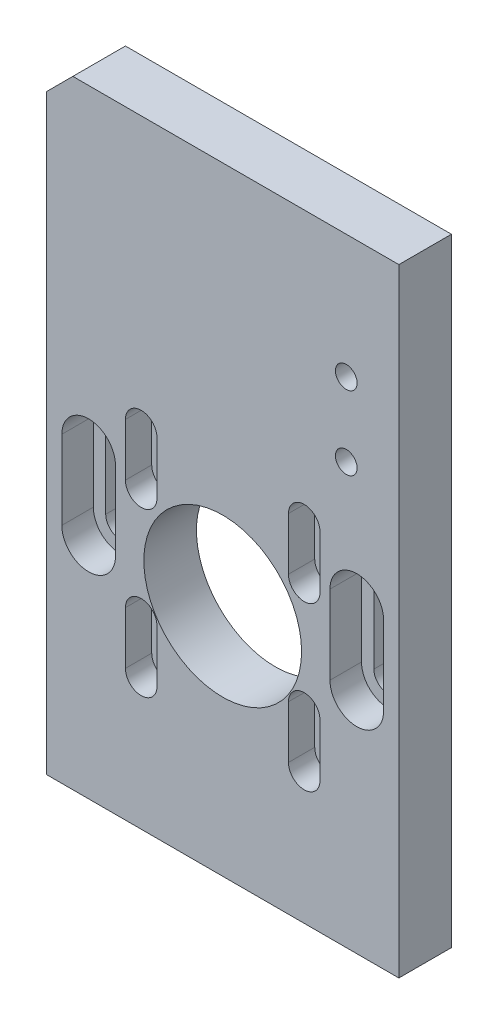
SolidWorks part; units mm, degrees
ref_plane "Front Plane" through (0, 0, 0) normal (0, 0, 1) x (1, 0, 0)
ref_plane "Top Plane" through (0, 0, 0) normal (0, 1, 0) x (1, 0, 0)
ref_plane "Right Plane" through (0, 0, 0) normal (1, 0, 0) x (0, 0, -1)
sketch "Sketch1" plane through (0, 0, 0) normal (0, 0, 1) x (1, 0, 0)
  line L0 (0, 0) -> (0, 98.1215) construction
  line L1 (-33.5, 0) -> (33.5, 0)
  line L2 (-33.5, 0) -> (-33.5, 112.5)
  line L3 (-28.5, 117.5) -> (33.5, 117.5)
  line L4 (33.5, 0) -> (33.5, 117.5)
  line L5 (-33.5, 112.5) -> (-28.5, 117.5)
  point P2 (-33.5, 117.5)
  point P7 (0, 0)
  dimension "D1" = 67
  dimension "D2" = 117.5
extrude "Boss-Extrude1" add sketch "Sketch1" along normal blind 10
sketch "Sketch2" plane through (0, 0, 10) normal (0, 0, 1) x (1, 0, 0)
  line L0 (-33.5, 0) -> (33.5, 0) construction
  line L2 (0, 0) -> (0, 83.1047) construction
  circle A0 centre (0, 44.5) radius 15
  dimension "D1" = 30
  dimension "D2" = 44.5
extrude "Motor Hole" cut sketch "Sketch2" against normal through all
sketch "Sketch3" plane through (0, 0, 10) normal (0, 0, 1) x (1, 0, 0)
  line L0 (-15.5, 66) -> (-15.5, 56) construction
  line L1 (-12.5, 66) -> (-12.5, 56)
  line L2 (-18.5, 66) -> (-18.5, 56)
  line L3 (-33.5, 112.5) -> (-33.5, 0) construction
  line L4 (-33.5, 0) -> (33.5, 0) construction
  arc A0 (-12.5, 66) -> (-18.5, 66) centre (-15.5, 66) ccw
  arc A1 (-18.5, 56) -> (-12.5, 56) centre (-15.5, 56) ccw
  point P2 (-15.5, 61)
  dimension "D1" = 3
  dimension "D4" = 56
  dimension "D2" = 10
  dimension "D3" = 15
extrude "Screw Hole" cut sketch "Sketch3" against normal blind 5
sketch "Sketch5" plane through (0, 0, 5) normal (0, 0, 1) x (1, 0, 0)
  line L4 (-17.25, 66) -> (-17.25, 56)
  line L5 (-13.75, 56) -> (-13.75, 66)
  line L6 (-17.25, 66) -> (-17.25, 56)
  line L7 (-13.75, 56) -> (-13.75, 66)
  arc A4 (-13.75, 66) -> (-17.25, 66) centre (-15.5, 66) ccw
  arc A5 (-17.25, 56) -> (-13.75, 56) centre (-15.5, 56) ccw
  arc A6 (-13.75, 66) -> (-17.25, 66) centre (-15.5, 66) ccw
  arc A7 (-17.25, 56) -> (-13.75, 56) centre (-15.5, 56) ccw
  dimension "D1" = 1.25
extrude "Cut-Extrude3" cut sketch "Sketch5" against normal through all
pattern_linear "LPattern1" count 2 spacing 31 along (1, 0, 0) count 2 spacing 31 along (0, -1, 0) of "Screw Hole", "Cut-Extrude3"
sketch "Sketch6" plane through (0, 0, 10) normal (0, 0, 1) x (1, 0, 0)
  line L0 (-25.5, 57.5) -> (-25.5, 42.5) construction
  line L1 (-20.4, 57.5) -> (-20.4, 42.5)
  line L2 (-30.6, 57.5) -> (-30.6, 42.5)
  line L3 (-33.5, 112.5) -> (-33.5, 0) construction
  line L5 (-33.5, 0) -> (33.5, 0) construction
  arc A0 (-20.4, 57.5) -> (-30.6, 57.5) centre (-25.5, 57.5) ccw
  arc A1 (-30.6, 42.5) -> (-20.4, 42.5) centre (-25.5, 42.5) ccw
  point P2 (-25.5, 50)
  dimension "D2" = 5.1
  dimension "D3" = 42.5
  dimension "D1" = 2.9
  dimension "D4" = 15
extrude "Cut-Extrude4" cut sketch "Sketch6" against normal blind 6
sketch "Sketch7" plane through (0, 0, 4) normal (0, 0, 1) x (1, 0, 0)
  line L4 (-28.25, 57.5) -> (-28.25, 42.5)
  line L5 (-22.75, 42.5) -> (-22.75, 57.5)
  line L6 (-28.25, 57.5) -> (-28.25, 42.5)
  line L7 (-22.75, 42.5) -> (-22.75, 57.5)
  arc A4 (-22.75, 57.5) -> (-28.25, 57.5) centre (-25.5, 57.5) ccw
  arc A5 (-28.25, 42.5) -> (-22.75, 42.5) centre (-25.5, 42.5) ccw
  arc A6 (-22.75, 57.5) -> (-28.25, 57.5) centre (-25.5, 57.5) ccw
  arc A7 (-28.25, 42.5) -> (-22.75, 42.5) centre (-25.5, 42.5) ccw
  dimension "D1" = 2.35
extrude "Cut-Extrude5" cut sketch "Sketch7" against normal through all
mirror "Mirror1" about plane through (0, 0, 0) normal (1, 0, 0) of "Cut-Extrude5", "Cut-Extrude4"
sketch "Sketch8" plane through (0, 0, 10) normal (0, 0, 1) x (1, 0, 0)
  line L0 (33.5, 0) -> (33.5, 117.5) construction
  line L1 (33.5, 117.5) -> (-28.5, 117.5) construction
  circle A0 centre (23.5, 94) radius 2.065
  circle A1 centre (23.5, 80) radius 2.065
  point P8 (23.5, 87.7761)
  point P9 (0, 0)
  dimension "D1" = 4.13
  dimension "D2" = 14
  dimension "D3" = 10
  dimension "D4" = 23.5
extrude "Cut-Extrude6" cut sketch "Sketch8" against normal through all
